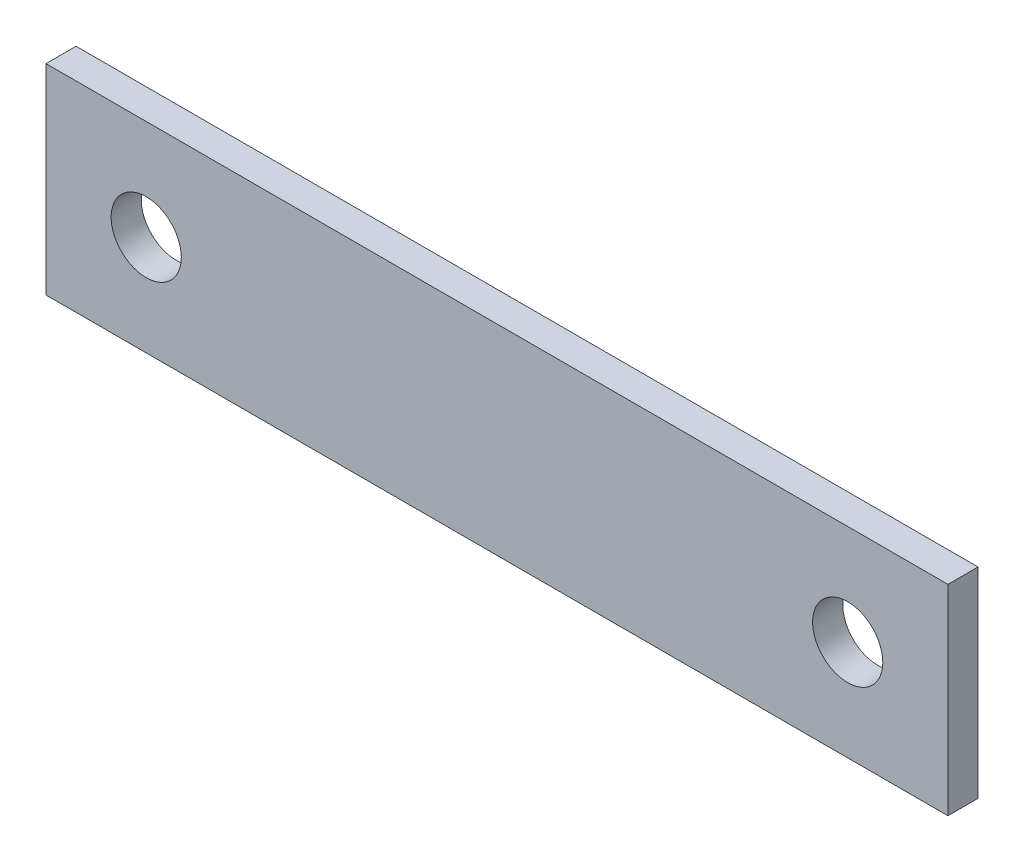
SolidWorks part; units mm, degrees
material "Acrílico (Impacto medio-alto)"
ref_plane "Alzado" through (0, 0, 0) normal (0, 0, 1) x (1, 0, 0)
ref_plane "Planta" through (0, 0, 0) normal (0, 1, 0) x (1, 0, 0)
ref_plane "Vista lateral" through (0, 0, 0) normal (1, 0, 0) x (0, 0, -1)
sketch "Croquis1" plane through (0, 0, 0) normal (0, 0, 1) x (1, 0, 0)
  line L1 (-81.8885, 26.0053) -> (8.1115, 26.0053)
  line L2 (-81.8885, 26.0053) -> (-81.8885, 6.0053)
  line L3 (-81.8885, 6.0053) -> (8.1115, 6.0053)
  line L4 (8.1115, 26.0053) -> (8.1115, 6.0053)
  circle A0 centre (-71.8885, 16.0053) radius 3.5
  circle A1 centre (-1.8885, 16.0053) radius 3.5
  dimension "D3" = 10
  dimension "D1" = 90
  dimension "D2" = 20
  dimension "D4" = 10
  dimension "D5" = 10
  dimension "D6" = 10
extrude "Saliente-Extruir1" add sketch "Croquis1" along normal blind 3
